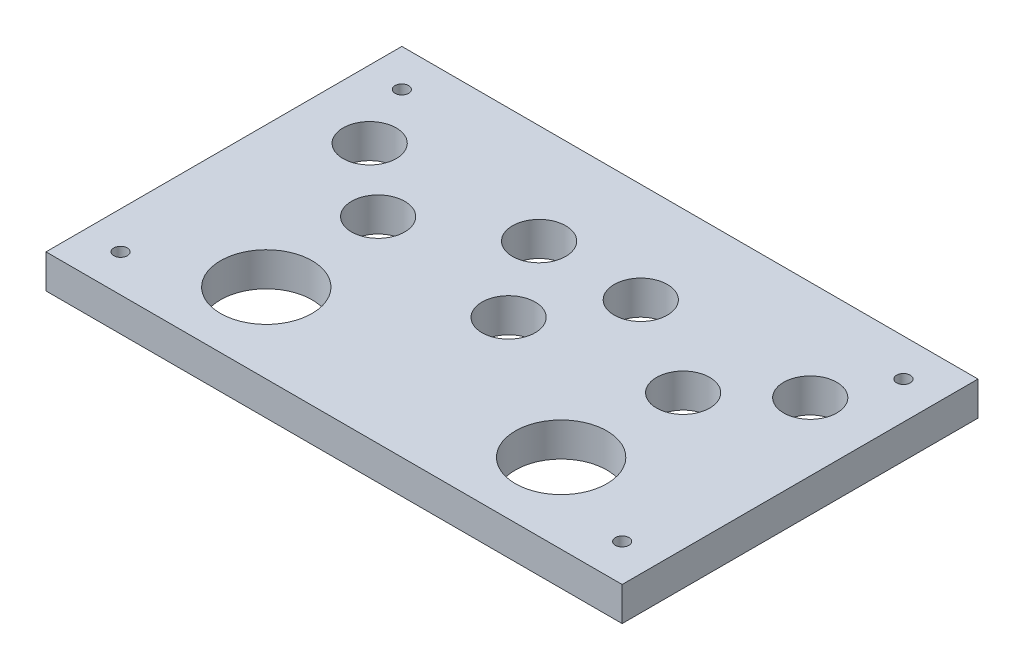
SolidWorks part; units mm, degrees
ref_plane "正面" through (0, 0, 0) normal (0, 0, 1) x (1, 0, 0)
ref_plane "平面" through (0, 0, 0) normal (0, 1, 0) x (1, 0, 0)
ref_plane "右側面" through (0, 0, 0) normal (1, 0, 0) x (0, 0, -1)
sketch "ｽｹｯﾁ1" plane through (0, 0, 0) normal (0, 1, 0) x (1, 0, 0)
  line L0 (85, 100) -> (85, 43.8318) construction
  line L1 (0, 0) -> (170, 0)
  line L2 (0, 0) -> (0, 105)
  line L3 (0, 105) -> (170, 105)
  line L4 (170, 0) -> (170, 105)
  line L5 (5, 100) -> (165, 100) construction
  line L6 (5, 100) -> (5, 5) construction
  line L7 (5, 5) -> (165, 5) construction
  line L8 (165, 100) -> (165, 5) construction
  line L9 (5, 52.5) -> (92.5057, 52.5) construction
  line L10 (25, 100) -> (5, 80) construction
  line L11 (58.33, 94.7) -> (111.67, 94.7)
  line L12 (58.33, 94.7) -> (58.33, 26.11)
  line L13 (58.33, 26.11) -> (111.67, 26.11)
  line L14 (111.67, 94.7) -> (111.67, 26.11)
  line L15 (57, 9) -> (23, 9)
  line L16 (57, 9) -> (57, 36)
  line L17 (57, 36) -> (23, 36)
  line L18 (23, 9) -> (23, 36)
  line L19 (25, 5) -> (5, 25) construction
  line L21 (113, 11) -> (147, 11)
  line L22 (113, 11) -> (113, 38)
  line L23 (113, 38) -> (147, 38)
  line L24 (147, 11) -> (147, 38)
  circle A0 centre (85, 51.5) radius 11
  circle A1 centre (70, 75.5) radius 11
  circle A2 centre (20, 75.5) radius 11
  circle A3 centre (40, 58) radius 11
  circle A4 centre (11, 94) radius 2
  circle A6 centre (11, 11) radius 2
  circle A7 centre (41.5, 23.5) radius 13.5
  circle A9 centre (159, 11) radius 2
  circle A12 centre (159, 94) radius 2
  circle A13 centre (128.5, 23.5) radius 13.5
  circle A14 centre (20, 75.5) radius 7.85
  circle A15 centre (40, 58) radius 7.85
  circle A16 centre (70, 75.5) radius 7.85
  circle A17 centre (85, 51.5) radius 7.85
  circle A18 centre (100, 75.5) radius 7.85
  circle A19 centre (130, 58) radius 7.85
  circle A20 centre (150, 75.5) radius 7.85
  point P17 (85, 94.7)
  dimension "D10" = 15.5
  dimension "D11" = 23
  dimension "D15" = 14.5
  dimension "D16" = 22
  dimension "D17" = 15
  dimension "D24" = 4
  dimension "D30" = 27
  dimension "D19" = 27
  dimension "D35" = 27
  dimension "D36" = 15.7
  dimension "D37" = 15.7
  dimension "D38" = 15.7
  dimension "D39" = 15.7
  dimension "D1" = 170
  dimension "D2" = 105
  dimension "D3" = 5
  dimension "D4" = 5
  dimension "D5" = 5
  dimension "D6" = 5
  dimension "D7" = 53.34
  dimension "D8" = 10.3
  dimension "D9" = 68.59
  dimension "D12" = 27
  dimension "D13" = 9
  dimension "D14" = 34
  dimension "D18" = 1
  dimension "D20" = 11
  dimension "D21" = 11
  dimension "D22" = 22
  dimension "D23" = 11
  dimension "D25" = 35
  dimension "D26" = 15
  dimension "D27" = 28
  dimension "D28" = 20
  dimension "D29" = 20
  dimension "D31" = 34
  dimension "D32" = 28
  dimension "D33" = 15.5
  dimension "D34" = 12.5
extrude "ﾎﾞｽ - 押し出し1" add sketch "ｽｹｯﾁ1" along normal blind 10 contours L1 L4 L3 L2 A19 A13 L21 L22 L23 L24 A6 A4 A3 A2 L11 L14 L13 L12 A7 L17 L16 L15 L18 A9 A12 A20 | A7 L17 L18 L15 L16 | A13 L21 L24 L23 L22 | A1 A16 | L14 L11 L12 L13 A0 A1 A18 | A2 A14 | A3 A15 | A0 A17
